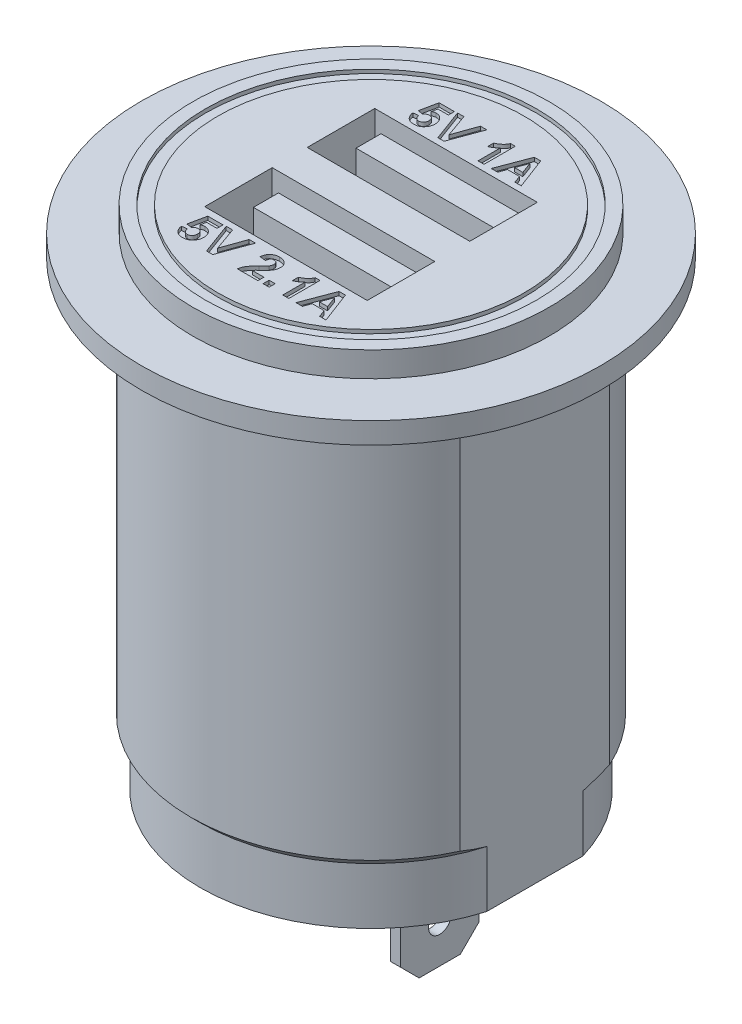
SolidWorks part; units mm, degrees
ref_plane "Спереди" through (0, 0, 0) normal (0, 0, 1) x (1, 0, 0)
ref_plane "Сверху" through (0, 0, 0) normal (0, 1, 0) x (1, 0, 0)
ref_plane "Справа" through (0, 0, 0) normal (1, 0, 0) x (0, 0, -1)
sketch "Эскиз1" plane through (0, 0, 0) normal (0, 0, 1) x (1, 0, 0)
  line L0 (0, 0) -> (0, 50.2484) construction
  line L1 (0, 0) -> (-13.65, 0)
  line L2 (-13.65, 0) -> (-13.65, 4.5)
  line L3 (-13.65, 4.5) -> (-14.4, 5.25)
  line L4 (-14.4, 5.25) -> (-14.4, 36.8)
  line L5 (-14.4, 36.8) -> (-18.35, 36.8)
  line L6 (-18.35, 36.8) -> (-18.35, 38.5)
  line L7 (-18.35, 38.5) -> (-14.25, 38.5)
  line L8 (-14.25, 38.5) -> (-14.25, 40.5)
  line L9 (-14.25, 40.5) -> (0, 40.5)
  line L10 (0, 0) -> (0, 40.5)
  dimension "D1" = 28.8
  dimension "D2" = 27.3
  dimension "D3" = 40.5
  dimension "D4" = 28.5
  dimension "D5" = 36.7
  dimension "D6" = 1.7
  dimension "D7" = 2
  dimension "D8" = 4.5
  dimension "D9" = 45
revolve "Повернуть1" add sketch "Эскиз1" angle 360 about L0
sketch "Эскиз2" plane through (0, 0, 0) normal (0, -1, 0) x (1, 0, 0)
  line L0 (0, 0) -> (0, 26.2243) construction
  line L1 (0, 0) -> (30.6636, 0) construction
  line L2 (-15.7, 5.9791) -> (-13.1, -5.9791) construction
  line L3 (15.7, -5.9791) -> (13.1, -5.9791)
  line L4 (15.7, -5.9791) -> (15.7, 5.9791)
  line L5 (15.7, 5.9791) -> (13.1, 5.9791)
  line L6 (13.1, -5.9791) -> (13.1, 5.9791)
  line L7 (15.7, -5.9791) -> (13.1, 5.9791) construction
  line L8 (15.7, 5.9791) -> (13.1, -5.9791) construction
  line L9 (-15.7, -5.9791) -> (-13.1, 5.9791) construction
  line L10 (-13.1, -5.9791) -> (-13.1, 5.9791)
  line L11 (-15.7, 5.9791) -> (-13.1, 5.9791)
  line L12 (-15.7, -5.9791) -> (-15.7, 5.9791)
  line L13 (-15.7, -5.9791) -> (-13.1, -5.9791)
  circle A0 centre (0, 0) radius 14.4 construction
  point P3 (14.4, 0)
  point P15 (-14.4, 0)
  dimension "D1" = 26.2
extrude "Вырез-Вытянуть1" cut sketch "Эскиз2" against normal up to surface (36.8 mm away) up to face at (0, 36.8, -14.4)
sketch "Эскиз3" plane through (0, 0, 0) normal (0, -1, 0) x (1, 0, 0)
  line L0 (0, 0) -> (0, 21.0145) construction
  line L1 (0, 0) -> (22.5019, 0) construction
  line L2 (-5.5, 3.15) -> (-4.7, -3.15) construction
  line L3 (5.5, -3.15) -> (4.7, -3.15)
  line L4 (5.5, -3.15) -> (5.5, 3.15)
  line L5 (5.5, 3.15) -> (4.7, 3.15)
  line L6 (4.7, -3.15) -> (4.7, 3.15)
  line L7 (5.5, -3.15) -> (4.7, 3.15) construction
  line L8 (5.5, 3.15) -> (4.7, -3.15) construction
  line L9 (-5.5, -3.15) -> (-4.7, 3.15) construction
  line L10 (-4.7, -3.15) -> (-4.7, 3.15)
  line L11 (-5.5, 3.15) -> (-4.7, 3.15)
  line L12 (-5.5, -3.15) -> (-5.5, 3.15)
  line L13 (-5.5, -3.15) -> (-4.7, -3.15)
  point P3 (5.1, 0)
  point P13 (-5.1, 0)
  dimension "D1" = 6.3
  dimension "D2" = 0.8
  dimension "D3" = 11
extrude "Бобышка-Вытянуть1" add sketch "Эскиз3" along normal blind 9.5
chamfer "Фаска1" distance 1.5 angle 45 4 edges at (5.1, -9.5, 3.15) (5.1, -9.5, -3.15) (-5.1, -9.5, 3.15) (-5.1, -9.5, -3.15)
sketch "Эскиз4" plane through (-5.5, 0, 0) normal (-1, 0, 0) x (0, 0, 1)
  line L0 (0, 0) -> (0, -9.5) construction
  line L1 (1.65, -9.5) -> (-1.65, -9.5) construction
  circle A0 centre (0, -6.4) radius 0.9
  dimension "D1" = 1.8
  dimension "D2" = 2.2
extrude "Вырез-Вытянуть2" cut sketch "Эскиз4" against normal through all
sketch "Эскиз5" plane through (0, 40.5, 0) normal (0, 1, 0) x (1, 0, 0)
  line L0 (0, 0) -> (0, 25.2082) construction
  line L1 (0, 0) -> (25.5927, 0) construction
  line L2 (-6.5, -1.4) -> (6.5, -6.8) construction
  line L3 (-6.5, 6.8) -> (6.5, 6.8)
  line L4 (-6.5, 6.8) -> (-6.5, 1.4)
  line L5 (-6.5, 1.4) -> (6.5, 1.4)
  line L6 (6.5, 6.8) -> (6.5, 1.4)
  line L7 (-6.5, 6.8) -> (6.5, 1.4) construction
  line L8 (-6.5, 1.4) -> (6.5, 6.8) construction
  line L9 (-6.5, -6.8) -> (6.5, -1.4) construction
  line L10 (6.5, -6.8) -> (6.5, -1.4)
  line L11 (-6.5, -1.4) -> (6.5, -1.4)
  line L12 (-6.5, -6.8) -> (-6.5, -1.4)
  line L13 (-6.5, -6.8) -> (6.5, -6.8)
  point P3 (0, 4.1)
  point P13 (0, -4.1)
  dimension "D1" = 13
  dimension "D2" = 5.4
  dimension "D3" = 2.8
extrude "Вырез-Вытянуть3" cut sketch "Эскиз5" against normal blind 10
sketch "Эскиз6" plane through (0, 30.5, 0) normal (0, 1, 0) x (1, 0, 0)
  line L0 (0, -6.8) -> (0, 6.8) construction
  line L1 (-6.5, -6.8) -> (6.5, -6.8) construction
  line L2 (6.5, 6.8) -> (-6.5, 6.8) construction
  line L3 (6.5, -1.4) -> (-6.5, -1.4) construction
  line L4 (5.5, 6.3) -> (-5.5, 6.3)
  line L5 (5.5, 6.3) -> (5.5, 4.3)
  line L6 (5.5, 4.3) -> (-5.5, 4.3)
  line L7 (-5.5, 6.3) -> (-5.5, 4.3)
  line L8 (5.5, 6.3) -> (-5.5, 4.3) construction
  line L9 (5.5, 4.3) -> (-5.5, 6.3) construction
  line L10 (5.5, -1.9) -> (-5.5, -1.9)
  line L11 (5.5, -1.9) -> (5.5, -3.9)
  line L12 (5.5, -3.9) -> (-5.5, -3.9)
  line L13 (-5.5, -1.9) -> (-5.5, -3.9)
  line L14 (5.5, -1.9) -> (-5.5, -3.9) construction
  line L15 (5.5, -3.9) -> (-5.5, -1.9) construction
  line L16 (6.5, 1.4) -> (6.5, 6.8) construction
  point P6 (0, 5.3)
  point P11 (0, -2.9)
  dimension "D1" = 0.5
  dimension "D2" = 0.5
  dimension "D3" = 1
  dimension "D4" = 2
extrude "Бобышка-Вытянуть2" add sketch "Эскиз6" along normal blind 9
sketch "Эскиз7" plane through (0, 40.5, 0) normal (0, 1, 0) x (1, 0, 0)
  line L0 (0, 0) -> (-26.3213, 0) construction
  line L1 (0, 0) -> (0, 23.5011) construction
  line L2 (-6.5, -6.8) -> (6.5, -6.8) construction
  line L3 (6.5, 6.8) -> (-6.5, 6.8) construction
  circle A0 centre (0, 0) radius 13.25 construction
  circle A1 centre (0, 0) radius 12.25 construction
  circle A2 centre (0, 0) radius 14.25 construction
  circle A3 centre (0, 0) radius 14.25 construction
  text T0 "5V 2.1A" font "Arial" height 2.5
  text T1 "5V 1A" font "Arial" height 2.5
  point P2 (1.5258, 0)
  point P13 (0, 0)
  point P17 (0, 0)
  dimension "D1" = 1
  dimension "D2" = 1
  dimension "D3" = 12.4
  dimension "D4" = 3
  dimension "D6" = 9.6
  dimension "D7" = 0.5
extrude "Вырез-Вытянуть4" cut sketch "Эскиз7" against normal blind 0.3
sketch "Эскиз8" plane through (0, 40.5, 0) normal (0, 1, 0) x (1, 0, 0)
  circle A0 centre (0, 0) radius 13.25 construction
  circle A1 centre (0, 0) radius 12.25 construction
  circle A2 centre (0, 0) radius 13.25
  circle A3 centre (0, 0) radius 12.25
extrude "Вырез-Вытянуть5" cut sketch "Эскиз8" against normal blind 0.3
